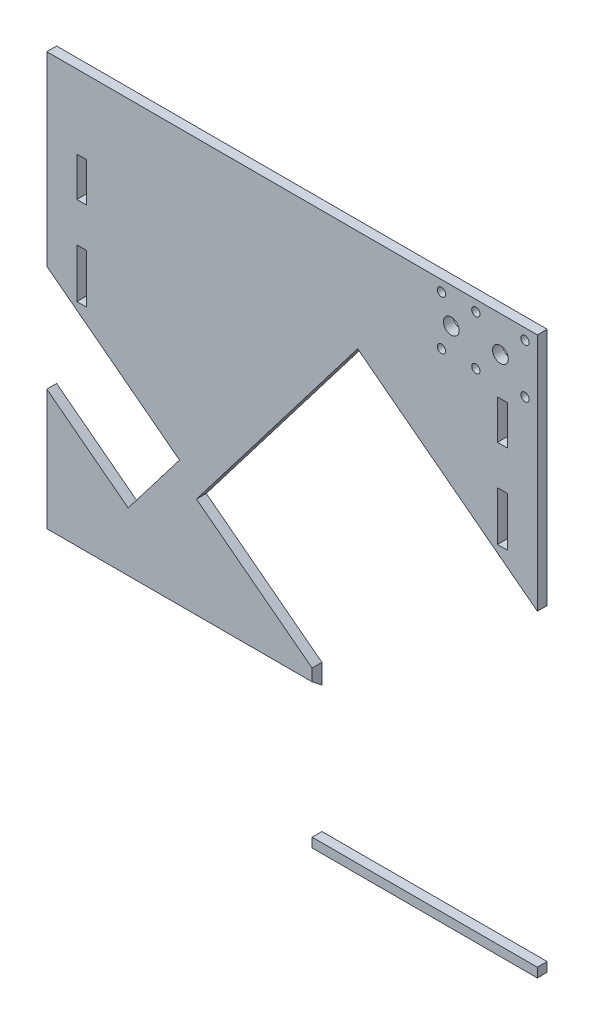
SolidWorks part; units mm, degrees
ref_plane "Front Plane" through (0, 0, 0) normal (0, 0, 1) x (1, 0, 0)
ref_plane "Top Plane" through (0, 0, 0) normal (0, 1, 0) x (1, 0, 0)
ref_plane "Right Plane" through (0, 0, 0) normal (1, 0, 0) x (0, 0, -1)
sketch "Sketch1" plane through (0, 0, 0) normal (0, 0, 1) x (1, 0, 0)
  line L0 (124.8, 0) -> (124.8, -283.36) construction
  line L1 (0, 0) -> (249.6, 0)
  line L2 (0, 0) -> (0, -283.36)
  line L3 (0, -283.36) -> (249.6, -283.36)
  line L4 (249.6, 0) -> (249.6, -283.36)
  dimension "D1" = 249.6
  dimension "D2" = 283.36
extrude "Boss-Extrude1" add sketch "Sketch1" along normal blind 5
sketch "Sketch2" plane through (0, 0, 5) normal (0, 0, 1) x (1, 0, 0)
  line L0 (-12.0438, -116.1701) -> (14.8299, 12.0438) construction
  line L1 (357.917, -193.7139) -> (384.7906, -65.5) construction
  line L2 (-12.0438, -116.1701) -> (357.917, -193.7139) construction
  line L3 (28.6688, 50.2813) -> (25.735, 46.2325) construction
  line L4 (25.735, 46.2325) -> (79.8591, 7.0134) construction
  line L5 (89.8056, 5.9807) -> (28.6688, 50.2813) construction
  line L6 (14.8299, 12.0438) -> (384.7906, -65.5) construction
  line L7 (14.2144, 9.1076) -> (384.1752, -68.4362) construction
  line L8 (-11.4283, -113.2339) -> (358.5324, -190.7777) construction
  line L9 (28.6688, 50.2813) -> (31.6026, 54.33) construction
  line L10 (31.6026, 54.33) -> (85.7267, 15.111) construction
  line L11 (236.1909, -165.1349) -> (261.8337, -42.7934) construction
  line L12 (126.6708, -78.3214) -> (249.0123, -103.9642) construction
  line L13 (113.8494, -139.4922) -> (139.4922, -17.1506) construction
  line L14 (249.6, 0) -> (0, 0) construction
  line L15 (0, 0) -> (0, -283.36) construction
  circle A0 centre (65.5, -65.5) radius 62.5 construction
  circle A1 centre (310.183, -116.7856) radius 62.5 construction
  circle A2 centre (65.5, -65.5) radius 65.5 construction
  circle A3 centre (187.8415, -91.1428) radius 62.5 construction
  circle A4 centre (89.8056, 5.9807) radius 75.5 construction
  circle A5 centre (89.8056, 5.9807) radius 2.5 construction
  circle A6 centre (69.5617, 20.6497) radius 1.5 construction
  arc A7 (79.8591, 7.0134) -> (85.7267, 15.111) centre (89.8056, 5.9807) ccw construction
  dimension "D1" = 125
  dimension "D2" = 125
  dimension "D3" = 5
  dimension "D6" = 3
  dimension "D7" = 10
  dimension "D10" = 125
  dimension "D8" = 3
  dimension "D4" = 5
  dimension "D5" = 25
  dimension "D9" = 5
sketch "Sketch3" plane through (0, -132.94, 103.8641) normal (0, 0.788, -0.6157) x (1, 0, 0)
  line L0 (135, 266.6158) -> (135, 56.7368) construction
  line L1 (135, 218.6086) -> (0, 218.6086)
  line L2 (135, 218.6086) -> (135, -11.4057)
  line L3 (135, -11.4057) -> (0, -11.4057)
  line L4 (0, 218.6086) -> (0, -11.4057)
  line L5 (0, 266.6158) -> (0, 56.7368) construction
extrude "Cut-Extrude1" cut sketch "Sketch3" against normal blind 193
sketch "Sketch4" plane through (0, 0, 5) normal (0, 0, 1) x (1, 0, 0)
  line L1 (214.957, -95.2783) -> (249.6, -121.7672)
  line L3 (249.6, -121.7672) -> (249.6, -278.6121)
  line L4 (54.8789, 27.1214) -> (359.1299, -205.5164) construction
  line L5 (135, -204.0831) -> (76.1492, -159.0843)
  line L6 (-27.1214, -80.1211) -> (277.1296, -312.7589) construction
  line L7 (76.1492, -159.0843) -> (158.1494, -51.8418)
  line L8 (79.1862, -155.1124) -> (155.1124, -55.8138) construction
  line L9 (158.1494, -51.8418) -> (214.957, -95.2783)
  line L10 (135, -340.9) -> (135, 0) construction
  line L11 (135, -204.0831) -> (135, -278.6121)
  line L12 (135, -278.6121) -> (249.6, -278.6121)
  line L13 (264.875, -278.6121) -> (5.125, -278.6121) construction
  line L14 (249.6, -161.5945) -> (249.6, 0) construction
extrude "Cut-Extrude2" cut sketch "Sketch4" against normal through all
sketch "Sketch5" plane through (0, 0, 5) normal (0, 0, 1) x (1, 0, 0)
  line L0 (0, -94.5647) -> (67.5231, -146.1945)
  line L1 (0, -94.5647) -> (-26.1186, -128.7234)
  line L2 (67.5231, -146.1945) -> (41.4045, -180.3532)
  line L3 (-26.1186, -128.7234) -> (41.4045, -180.3532)
  line L4 (0, 0) -> (0, -210.1812) construction
  line L5 (-24.0843, -76.1492) -> (280.1666, -308.787) construction
  dimension "D1" = 85
  dimension "D2" = 43
extrude "Cut-Extrude3" cut sketch "Sketch5" against normal through all
sketch "Sketch6" plane through (0, 0, 5) normal (0, 0, 1) x (1, 0, 0)
  circle A0 centre (243.3, -5.5) radius 2.1
  circle A1 centre (243.3, -30.5) radius 2.1
  circle A2 centre (218.3, -30.5) radius 2.1
  circle A3 centre (218.3, -5.5) radius 2.1
  circle A4 centre (200.8, -30.5) radius 2.1
  circle A5 centre (200.8, -5.5) radius 2.1
  circle A6 centre (243.3, -5.5) radius 2.1 construction
  circle A7 centre (218.3, -5.5) radius 2.1 construction
  circle A8 centre (243.3, -30.5) radius 2.1 construction
  circle A9 centre (218.3, -30.5) radius 2.1 construction
  circle A10 centre (200.8, -30.5) radius 2.1 construction
  circle A11 centre (200.8, -5.5) radius 2.1 construction
  circle A12 centre (205.8, -18) radius 4
  circle A13 centre (230.8, -18) radius 4
  circle A14 centre (205.8, -18) radius 4 construction
  circle A15 centre (230.8, -18) radius 4 construction
extrude "Cut-Extrude4" cut sketch "Sketch6" against normal through all
sketch "Sketch7" plane through (0, 0, 5) normal (0, 0, 1) x (1, 0, 0)
  line L0 (124.8, -7.0792) -> (124.8, -189.5476) construction
  line L1 (15.2882, -37.4779) -> (20.2882, -37.4779)
  line L2 (15.2882, -37.4779) -> (15.2882, -57.4779)
  line L3 (15.2882, -57.4779) -> (20.2882, -57.4779)
  line L4 (20.2882, -37.4779) -> (20.2882, -57.4779)
  line L5 (229.3118, -37.4779) -> (234.3118, -37.4779)
  line L6 (229.3118, -37.4779) -> (229.3118, -57.4779)
  line L7 (229.3118, -57.4779) -> (234.3118, -57.4779)
  line L8 (234.3118, -37.4779) -> (234.3118, -57.4779)
  line L9 (15.2882, -77.4779) -> (20.2882, -77.4779)
  line L10 (15.2882, -77.4779) -> (15.2882, -102.4779)
  line L11 (15.2882, -102.4779) -> (20.2882, -102.4779)
  line L12 (20.2882, -77.4779) -> (20.2882, -102.4779)
  line L13 (229.3118, -77.4779) -> (234.3118, -77.4779)
  line L14 (229.3118, -77.4779) -> (229.3118, -102.4779)
  line L15 (229.3118, -102.4779) -> (234.3118, -102.4779)
  line L16 (234.3118, -77.4779) -> (234.3118, -102.4779)
  line L17 (17.7882, -37.4779) -> (17.7882, -160.2371) construction
  line L18 (231.8118, -37.4779) -> (231.8118, -160.4946) construction
  line L20 (249.6, -121.7672) -> (249.6, 0) construction
  line L21 (0, 0) -> (0, -94.5647) construction
  line L22 (67.5231, -146.1945) -> (0, -94.5647) construction
  line L23 (249.6, -121.7672) -> (158.1494, -51.8418) construction
  dimension "D1" = 5
  dimension "D2" = 20
  dimension "D3" = 5
  dimension "D4" = 20
  dimension "D5" = 5
  dimension "D6" = 25
  dimension "D7" = 5
  dimension "D8" = 25
  dimension "D9" = 20
  dimension "D10" = 20
  dimension "D11" = 3
  dimension "D12" = 3
extrude "Cut-Extrude5" cut sketch "Sketch7" against normal through all
